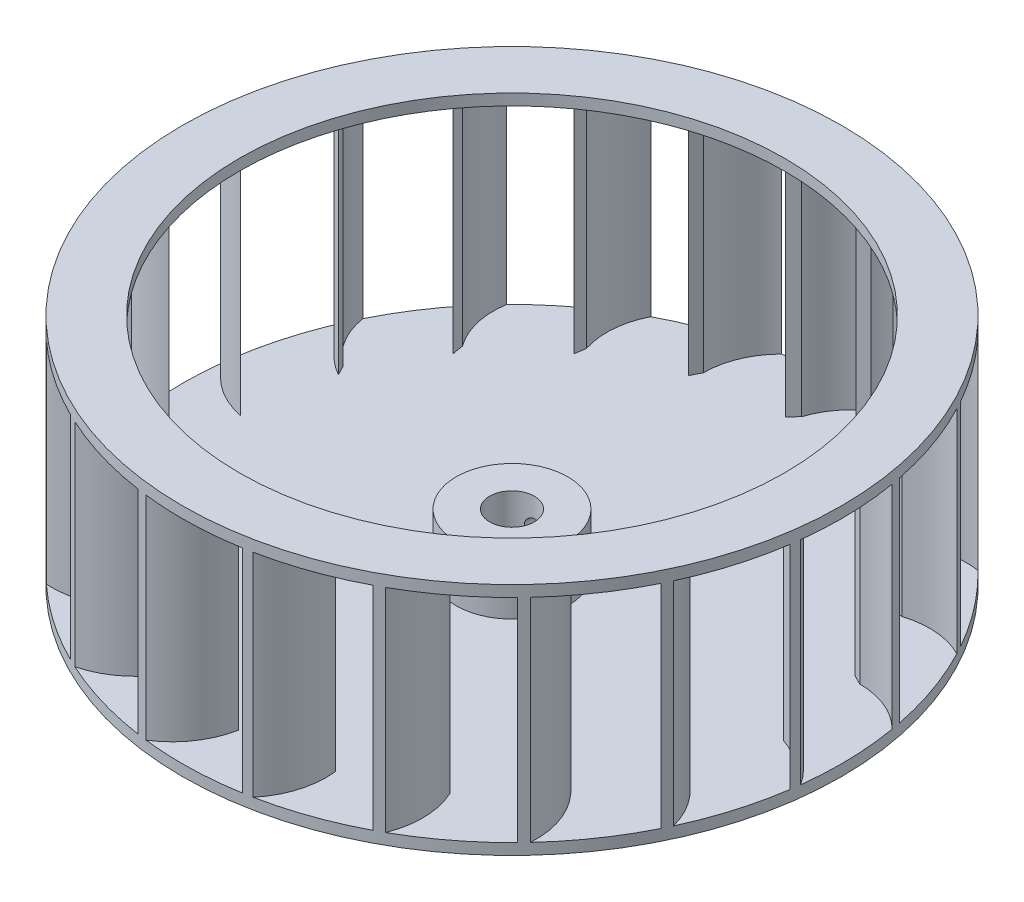
SolidWorks part; units mm, degrees
material "1060 Alloy"
ref_plane "Front Plane" through (0, 0, 0) normal (0, 0, 1) x (1, 0, 0)
ref_plane "Top Plane" through (0, 0, 0) normal (0, 1, 0) x (1, 0, 0)
ref_plane "Right Plane" through (0, 0, 0) normal (1, 0, 0) x (0, 0, -1)
sketch "Sketch2" plane through (0, 0, 0) normal (0, 1, 0) x (1, 0, 0)
  circle A0 centre (0, 0) radius 59
  dimension "D1" = 118
extrude "Boss-Extrude1" add sketch "Sketch2" along normal blind 2
sketch "Sketch3" plane through (0, 2, 0) normal (0, 1, 0) x (1, 0, 0)
  line L0 (-14.8929, 46.4744) -> (-14, 48.2641)
  line L1 (0, 48.2641) -> (0, 0) construction
  line L2 (-9.8995, 58.1636) -> (0, 48.2641) construction
  line L3 (0, 48.2641) -> (-33.9349, 48.2641) construction
  line L4 (0.1974, 48.802) -> (1.5996, 50.2281)
  line L5 (15.2684, 46.3524) -> (17.0427, 47.2754)
  line L6 (28.8448, 39.3656) -> (30.8175, 39.6951)
  line L7 (39.5977, 28.5253) -> (41.5756, 28.2292)
  line L8 (46.4744, 14.8929) -> (48.2641, 14)
  line L9 (48.802, -0.1974) -> (50.2281, -1.5996)
  line L10 (46.3524, -15.2684) -> (47.2754, -17.0427)
  line L11 (39.3656, -28.8448) -> (39.6951, -30.8175)
  line L12 (28.5253, -39.5977) -> (28.2292, -41.5756)
  line L13 (14.8929, -46.4744) -> (14, -48.2641)
  line L14 (-0.1974, -48.802) -> (-1.5996, -50.2281)
  line L15 (-15.2684, -46.3524) -> (-17.0427, -47.2754)
  line L16 (-28.8448, -39.3656) -> (-30.8175, -39.6951)
  line L17 (-39.5977, -28.5253) -> (-41.5756, -28.2292)
  line L18 (-46.4744, -14.8929) -> (-48.2641, -14)
  line L19 (-48.802, 0.1974) -> (-50.2281, 1.5996)
  line L20 (-46.3524, 15.2684) -> (-47.2754, 17.0427)
  line L21 (-39.3656, 28.8448) -> (-39.6951, 30.8175)
  line L22 (-28.5253, 39.5977) -> (-28.2292, 41.5756)
  arc A0 (-11.5264, 57.8631) -> (-14.8929, 46.4744) centre (0, 48.2641) ccw
  circle A1 centre (0, 0) radius 59 construction
  arc A2 (-9.8995, 58.1636) -> (-14, 48.2641) centre (0, 48.2641) ccw
  arc A3 (-11.5264, 57.8631) -> (-9.8995, 58.1636) centre (0, 0) cw
  arc A4 (6.9184, 58.593) -> (0.1974, 48.802) centre (14.9144, 45.9019) ccw
  arc A5 (8.5586, 58.3759) -> (1.5996, 50.2281) centre (14.9144, 45.9019) ccw
  arc A6 (6.9184, 58.593) -> (8.5586, 58.3759) centre (0, 0) cw
  arc A7 (24.686, 53.5873) -> (15.2684, 46.3524) centre (28.3689, 39.0465) ccw
  arc A8 (26.1788, 52.8741) -> (17.0427, 47.2754) centre (28.3689, 39.0465) ccw
  arc A9 (24.686, 53.5873) -> (26.1788, 52.8741) centre (0, 0) cw
  arc A10 (40.0372, 43.3362) -> (28.8448, 39.3656) centre (39.0465, 28.3689) ccw
  arc A11 (41.2365, 42.1965) -> (30.8175, 39.6951) centre (39.0465, 28.3689) ccw
  arc A12 (40.0372, 43.3362) -> (41.2365, 42.1965) centre (0, 0) cw
  arc A13 (51.4693, 28.843) -> (39.5977, 28.5253) centre (45.9019, 14.9144) ccw
  arc A14 (52.2577, 27.3885) -> (41.5756, 28.2292) centre (45.9019, 14.9144) ccw
  arc A15 (51.4693, 28.843) -> (52.2577, 27.3885) centre (0, 0) cw
  arc A16 (57.8631, 11.5264) -> (46.4744, 14.8929) centre (48.2641, 0) ccw
  arc A17 (58.1636, 9.8995) -> (48.2641, 14) centre (48.2641, 0) ccw
  arc A18 (57.8631, 11.5264) -> (58.1636, 9.8995) centre (0, 0) cw
  arc A19 (58.593, -6.9184) -> (48.802, -0.1974) centre (45.9019, -14.9144) ccw
  arc A20 (58.3759, -8.5586) -> (50.2281, -1.5996) centre (45.9019, -14.9144) ccw
  arc A21 (58.593, -6.9184) -> (58.3759, -8.5586) centre (0, 0) cw
  arc A22 (53.5873, -24.686) -> (46.3524, -15.2684) centre (39.0465, -28.3689) ccw
  arc A23 (52.8741, -26.1788) -> (47.2754, -17.0427) centre (39.0465, -28.3689) ccw
  arc A24 (53.5873, -24.686) -> (52.8741, -26.1788) centre (0, 0) cw
  arc A25 (43.3362, -40.0372) -> (39.3656, -28.8448) centre (28.3689, -39.0465) ccw
  arc A26 (42.1965, -41.2365) -> (39.6951, -30.8175) centre (28.3689, -39.0465) ccw
  arc A27 (43.3362, -40.0372) -> (42.1965, -41.2365) centre (0, 0) cw
  arc A28 (28.843, -51.4693) -> (28.5253, -39.5977) centre (14.9144, -45.9019) ccw
  arc A29 (27.3885, -52.2577) -> (28.2292, -41.5756) centre (14.9144, -45.9019) ccw
  arc A30 (28.843, -51.4693) -> (27.3885, -52.2577) centre (0, 0) cw
  arc A31 (11.5264, -57.8631) -> (14.8929, -46.4744) centre (0, -48.2641) ccw
  arc A32 (9.8995, -58.1636) -> (14, -48.2641) centre (0, -48.2641) ccw
  arc A33 (11.5264, -57.8631) -> (9.8995, -58.1636) centre (0, 0) cw
  arc A34 (-6.9184, -58.593) -> (-0.1974, -48.802) centre (-14.9144, -45.9019) ccw
  arc A35 (-8.5586, -58.3759) -> (-1.5996, -50.2281) centre (-14.9144, -45.9019) ccw
  arc A36 (-6.9184, -58.593) -> (-8.5586, -58.3759) centre (0, 0) cw
  arc A37 (-24.686, -53.5873) -> (-15.2684, -46.3524) centre (-28.3689, -39.0465) ccw
  arc A38 (-26.1788, -52.8741) -> (-17.0427, -47.2754) centre (-28.3689, -39.0465) ccw
  arc A39 (-24.686, -53.5873) -> (-26.1788, -52.8741) centre (0, 0) cw
  arc A40 (-40.0372, -43.3362) -> (-28.8448, -39.3656) centre (-39.0465, -28.3689) ccw
  arc A41 (-41.2365, -42.1965) -> (-30.8175, -39.6951) centre (-39.0465, -28.3689) ccw
  arc A42 (-40.0372, -43.3362) -> (-41.2365, -42.1965) centre (0, 0) cw
  arc A43 (-51.4693, -28.843) -> (-39.5977, -28.5253) centre (-45.9019, -14.9144) ccw
  arc A44 (-52.2577, -27.3885) -> (-41.5756, -28.2292) centre (-45.9019, -14.9144) ccw
  arc A45 (-51.4693, -28.843) -> (-52.2577, -27.3885) centre (0, 0) cw
  arc A46 (-57.8631, -11.5264) -> (-46.4744, -14.8929) centre (-48.2641, 0) ccw
  arc A47 (-58.1636, -9.8995) -> (-48.2641, -14) centre (-48.2641, 0) ccw
  arc A48 (-57.8631, -11.5264) -> (-58.1636, -9.8995) centre (0, 0) cw
  arc A49 (-58.593, 6.9184) -> (-48.802, 0.1974) centre (-45.9019, 14.9144) ccw
  arc A50 (-58.3759, 8.5586) -> (-50.2281, 1.5996) centre (-45.9019, 14.9144) ccw
  arc A51 (-58.593, 6.9184) -> (-58.3759, 8.5586) centre (0, 0) cw
  arc A52 (-53.5873, 24.686) -> (-46.3524, 15.2684) centre (-39.0465, 28.3689) ccw
  arc A53 (-52.8741, 26.1788) -> (-47.2754, 17.0427) centre (-39.0465, 28.3689) ccw
  arc A54 (-53.5873, 24.686) -> (-52.8741, 26.1788) centre (0, 0) cw
  arc A55 (-43.3362, 40.0372) -> (-39.3656, 28.8448) centre (-28.3689, 39.0465) ccw
  arc A56 (-42.1965, 41.2365) -> (-39.6951, 30.8175) centre (-28.3689, 39.0465) ccw
  arc A57 (-43.3362, 40.0372) -> (-42.1965, 41.2365) centre (0, 0) cw
  arc A58 (-28.843, 51.4693) -> (-28.5253, 39.5977) centre (-14.9144, 45.9019) ccw
  arc A59 (-27.3885, 52.2577) -> (-28.2292, 41.5756) centre (-14.9144, 45.9019) ccw
  arc A60 (-28.843, 51.4693) -> (-27.3885, 52.2577) centre (0, 0) cw
  dimension "D1" = 14
  dimension "D2" = 15
  dimension "D3" = 2
  dimension "D4" = 45
  dimension "D5" = 20
extrude "Boss-Extrude2" add sketch "Sketch3" along normal blind 38
sketch "Sketch4" plane through (0, 40, 0) normal (0, 1, 0) x (1, 0, 0)
  circle A0 centre (0, 0) radius 59
  circle A1 centre (0, 0) radius 48.8024
  circle A2 centre (0, 0) radius 59 construction
extrude "Boss-Extrude3" add sketch "Sketch4" along normal blind 2
sketch "Sketch5" plane through (0, 2, 0) normal (0, 1, 0) x (1, 0, 0)
  circle A0 centre (0, 0) radius 10
  circle A1 centre (0, 0) radius 4
  dimension "D1" = 8
  dimension "D2" = 20
extrude "Boss-Extrude4" add sketch "Sketch5" along normal blind 10
sketch "Sketch6" plane through (0, 0, 0) normal (0, 0, 1) x (1, 0, 0)
  line L0 (0, 12) -> (0, 2) construction
  line L1 (10, 12) -> (-10, 12) construction
  line L2 (9.8995, 2) -> (-6.9184, 2) construction
  circle A0 centre (0, 7) radius 1.5
  point P9 (0, 0)
  dimension "D1" = 3
extrude "Cut-Extrude1" cut sketch "Sketch6" against normal blind 25
sketch "Sketch7" plane through (0, 2, 0) normal (0, 1, 0) x (1, 0, 0)
  circle A1 centre (0, 0) radius 4
  circle A2 centre (0, 0) radius 4
  dimension "D1" = 0
extrude "Cut-Extrude2" cut sketch "Sketch7" against normal through all
